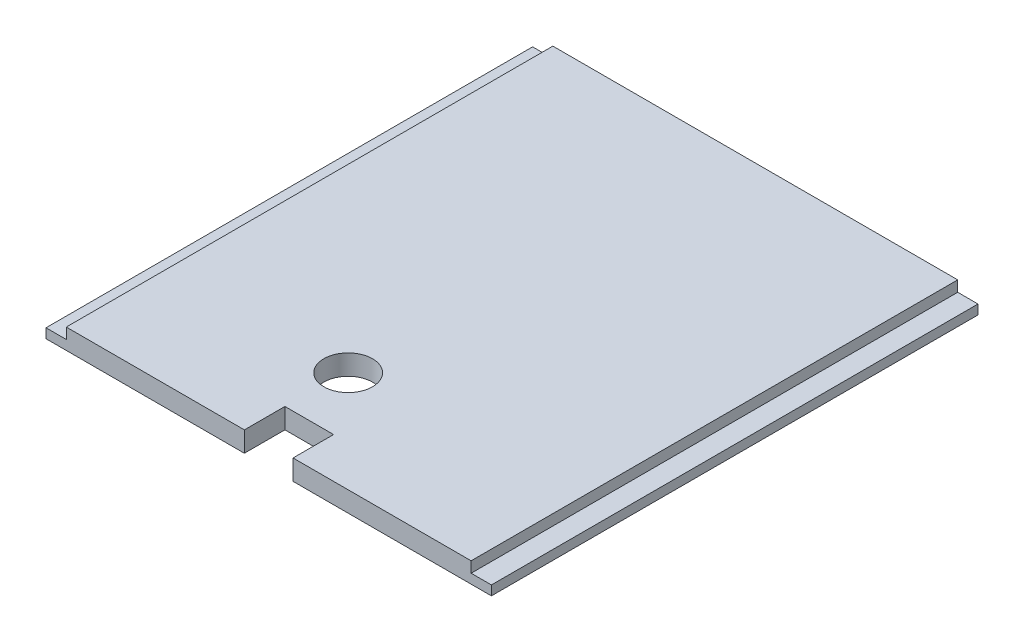
SolidWorks part; units mm, degrees
ref_plane "Front Plane" through (0, 0, 0) normal (0, 0, 1) x (1, 0, 0)
ref_plane "Top Plane" through (0, 0, 0) normal (0, 1, 0) x (1, 0, 0)
ref_plane "Right Plane" through (0, 0, 0) normal (1, 0, 0) x (0, 0, -1)
sketch "Sketch1" plane through (0, 0, 0) normal (0, 1, 0) x (1, 0, 0)
  line L1 (0, 0) -> (139.5, 0)
  line L2 (0, 0) -> (0, 152.4)
  line L3 (0, 152.4) -> (139.5, 152.4)
  line L4 (139.5, 0) -> (139.5, 152.4)
  dimension "D1" = 152.4
  dimension "D2" = 139.5
extrude "Boss-Extrude1" add sketch "Sketch1" along normal blind 6.35
sketch "Sketch2" plane through (0, 6.35, 0) normal (0, 1, 0) x (1, 0, 0)
  line L0 (0, 0) -> (139.5, 0) construction
  line L1 (0, 152.4) -> (6.35, 152.4)
  line L2 (0, 152.4) -> (0, 0)
  line L3 (0, 0) -> (6.35, 0)
  line L4 (6.35, 152.4) -> (6.35, 0)
  line L6 (139.5, 152.4) -> (133.15, 152.4)
  line L7 (139.5, 152.4) -> (139.5, 0)
  line L8 (139.5, 0) -> (133.15, 0)
  line L9 (133.15, 152.4) -> (133.15, 0)
  dimension "D1" = 6.35
  dimension "D2" = 6.35
extrude "Cut-Extrude1" cut sketch "Sketch2" against normal blind 3.375
sketch "Sketch3" plane through (0, 6.35, 0) normal (0, 1, 0) x (1, 0, 0)
  line L0 (6.35, 0) -> (133.15, 0) construction
  line L1 (62.13, 0) -> (77.37, 0)
  line L2 (62.13, 0) -> (62.13, 12.7)
  line L3 (62.13, 12.7) -> (77.37, 12.7)
  line L4 (77.37, 0) -> (77.37, 12.7)
  line L5 (62.13, 12.7) -> (6.35, 12.7) construction
  line L6 (6.35, 0) -> (6.35, 152.4) construction
  line L7 (77.37, 12.7) -> (133.15, 12.7) construction
  line L8 (133.15, 152.4) -> (133.15, 0) construction
  line L9 (69.75, 0) -> (69.75, 46.0391) construction
  circle A0 centre (62.892, 31.75) radius 7.62
  dimension "D5" = 15.24
  dimension "D1" = 15.24
  dimension "D2" = 12.7
  dimension "D3" = 31.75
  dimension "D4" = 6.858
extrude "Cut-Extrude2" cut sketch "Sketch3" against normal through all
